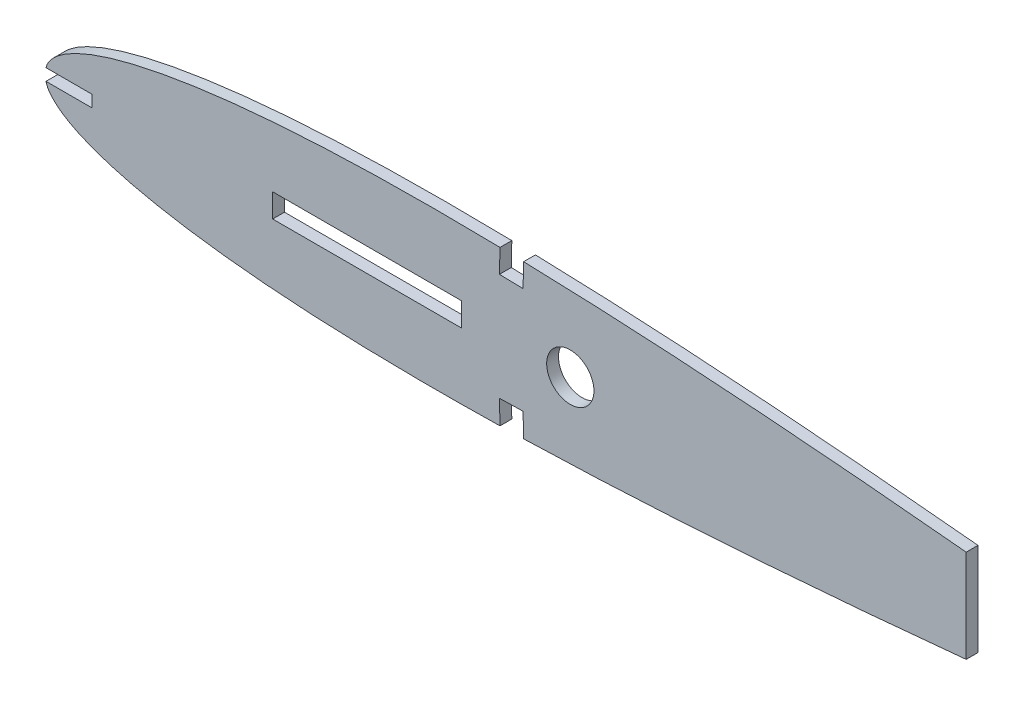
SolidWorks part; units mm, degrees
material "Plywood"
ref_plane "Front Plane" through (0, 0, 0) normal (0, 0, 1) x (1, 0, 0)
ref_plane "Top Plane" through (0, 0, 0) normal (0, 1, 0) x (1, 0, 0)
ref_plane "Right Plane" through (0, 0, 0) normal (1, 0, 0) x (0, 0, -1)
curve "Curve1"
  spline degree 3 poles (318.77, 0, 0) (318.6165, 0.178, 0) (318.1279, 0.7447, 0) (316.4159, 0.5798, 0) (314.0794, 1.1239, 0) (310.6457, 1.4976, 0) (306.3402, 2.1168, 0) (301.1057, 2.7975, 0) (295.0055, 3.5941, 0) (288.0665, 4.472, 0) (280.335, 5.4268, 0) (271.8575, 6.4421, 0) (262.6867, 7.5062, 0) (252.8789, 8.6045, 0) (242.4947, 9.7236, 0) (231.5982, 10.8496, 0) (220.2564, 11.9679, 0) (208.5394, 13.0629, 0) (196.5193, 14.1202, 0) (184.2704, 15.122, 0) (171.8679, 16.0521, 0) (159.3884, 16.8933, 0) (146.9087, 17.6278, 0) (134.5058, 18.2372, 0) (122.2562, 18.7052, 0) (110.2351, 19.0165, 0) (98.5168, 19.156, 0) (87.1732, 19.1125, 0) (76.2743, 18.8777, 0) (65.8873, 18.4456, 0) (56.076, 17.8151, 0) (46.9007, 16.9881, 0) (38.4176, 15.971, 0) (30.6784, 14.7725, 0) (23.7299, 13.4051, 0) (17.6134, 11.8842, 0) (12.3615, 10.2248, 0) (8.0073, 8.4423, 0) (4.5466, 6.5486, 0) (2.0351, 4.5401, 0) (0.333, 2.3682, 0) (0.1059, 0.7528, 0) (0, 0, 0) knots 0 0 0 0 0.002092 0.00666 0.01424 0.024785 0.038227 0.054481 0.073445 0.094999 0.119006 0.145319 0.17377 0.204184 0.236371 0.270129 0.30525 0.341517 0.378701 0.416575 0.454902 0.493447 0.531971 0.570237 0.608013 0.645066 0.681178 0.71613 0.749718 0.781748 0.812037 0.840415 0.866732 0.890849 0.912652 0.932046 0.948973 0.963413 0.975421 0.985175 0.993091 1 1 1 1
sketch "Sketch2" plane through (0, 0, 0) normal (0, 0, 1) x (1, 0, 0)
  line L4 (0, 0) -> (349.25, 0) construction
  spline S1 degree 3 poles (349.25, 0) (349.0818, 0.195) (348.5465, 0.8159) (346.6708, 0.6353) (344.1109, 1.2313) (340.3489, 1.6408) (335.6317, 2.3192) (329.8967, 3.065) (323.2132, 3.9378) (315.6107, 4.8996) (307.1399, 5.9457) (297.8518, 7.058) (287.8042, 8.224) (277.0586, 9.4273) (265.6815, 10.6534) (253.743, 11.887) (241.3168, 13.1123) (228.4795, 14.3119) (215.31, 15.4703) (201.8899, 16.5679) (188.3015, 17.587) (174.6287, 18.5086) (160.9558, 19.3133) (147.3669, 19.981) (133.9461, 20.4937) (120.7755, 20.8348) (107.9367, 20.9876) (95.5085, 20.94) (83.5675, 20.6828) (72.1873, 20.2093) (61.4378, 19.5185) (51.3852, 18.6124) (42.091, 17.4981) (33.6118, 16.185) (25.9989, 14.6868) (19.2975, 13.0206) (13.5435, 11.2025) (8.7729, 9.2495) (4.9814, 7.1748) (2.2297, 4.9742) (0.3649, 2.5947) (0.116, 0.8248) (0, 0) knots 0 0 0 0 0.002092 0.00666 0.01424 0.024785 0.038227 0.054481 0.073445 0.094999 0.119006 0.145319 0.17377 0.204184 0.236371 0.270129 0.30525 0.341517 0.378701 0.416575 0.454902 0.493447 0.531971 0.570237 0.608013 0.645066 0.681178 0.71613 0.749718 0.781748 0.812037 0.840415 0.866732 0.890849 0.912652 0.932046 0.948973 0.963413 0.975421 0.985175 0.993091 1 1 1 1
  spline S2 degree 3 poles (349.25, 0) (349.0818, -0.195) (348.5465, -0.8159) (346.6708, -0.6353) (344.1109, -1.2313) (340.3489, -1.6408) (335.6317, -2.3192) (329.8967, -3.065) (323.2132, -3.9378) (315.6107, -4.8996) (307.1399, -5.9457) (297.8518, -7.058) (287.8042, -8.224) (277.0586, -9.4273) (265.6815, -10.6534) (253.743, -11.887) (241.3168, -13.1123) (228.4795, -14.3119) (215.31, -15.4703) (201.8899, -16.5679) (188.3015, -17.587) (174.6287, -18.5086) (160.9558, -19.3133) (147.3669, -19.981) (133.9461, -20.4937) (120.7755, -20.8348) (107.9367, -20.9876) (95.5085, -20.94) (83.5675, -20.6828) (72.1873, -20.2093) (61.4378, -19.5185) (51.3852, -18.6124) (42.091, -17.4981) (33.6118, -16.185) (25.9989, -14.6868) (19.2975, -13.0206) (13.5435, -11.2025) (8.7729, -9.2495) (4.9814, -7.1748) (2.2297, -4.9742) (0.3649, -2.5947) (0.116, -0.8248) (0, 0) knots 0 0 0 0 0.002092 0.00666 0.01424 0.024785 0.038227 0.054481 0.073445 0.094999 0.119006 0.145319 0.17377 0.204184 0.236371 0.270129 0.30525 0.341517 0.378701 0.416575 0.454902 0.493447 0.531971 0.570237 0.608013 0.645066 0.681178 0.71613 0.749718 0.781748 0.812037 0.840415 0.866732 0.890849 0.912652 0.932046 0.948973 0.963413 0.975421 0.985175 0.993091 1 1 1 1
  dimension "D1" = 349.25
extrude "Boss-Extrude1" add sketch "Sketch2" along normal blind 3.175
sketch "Sketch3" plane through (0, 0, 3.175) normal (0, 0, 1) x (1, 0, 0)
  line L0 (0, 0) -> (141.224, 0) construction
  line L1 (349.25, 50.8) -> (247.65, 50.8)
  line L2 (349.25, 50.8) -> (349.25, -50.8)
  line L3 (349.25, -50.8) -> (247.65, -50.8)
  line L4 (247.65, 50.8) -> (247.65, -50.8)
  line L5 (0, 1.5875) -> (12.7, 1.5875)
  line L6 (0, 1.5875) -> (0, -1.5875)
  line L7 (0, -1.5875) -> (12.7, -1.5875)
  line L8 (12.7, 1.5875) -> (12.7, -1.5875)
  line L9 (128.6754, -20.6224) -> (128.524, -14.2742)
  line L10 (128.6754, -20.6224) -> (122.3272, -20.7738) construction
  line L11 (128.524, -14.2742) -> (122.1758, -14.4256)
  line L12 (122.3272, -20.7738) -> (122.1758, -14.4256)
  line L13 (122.3272, -20.7738) -> (128.6754, -20.6224) construction
  line L14 (122.3272, -20.7738) -> (122.6301, -33.4702)
  line L15 (128.6754, -20.6224) -> (128.9783, -33.3188)
  line L16 (122.6301, -33.4702) -> (128.9783, -33.3188)
  line L17 (128.524, 14.2742) -> (122.1758, 14.4256)
  line L18 (128.524, 14.2742) -> (128.6754, 20.6224)
  line L19 (122.1758, 14.4256) -> (122.3272, 20.7738)
  line L20 (128.6754, 20.6224) -> (122.3272, 20.7738) construction
  line L21 (122.3272, 20.7738) -> (128.6754, 20.6224) construction
  line L22 (122.3272, 20.7738) -> (122.5522, 30.2059)
  line L23 (128.6754, 20.6224) -> (128.9004, 30.0545)
  line L24 (122.5522, 30.2059) -> (128.9004, 30.0545)
  circle A0 centre (141.224, 0) radius 6.35
  spline S0 degree 3 poles (0, 0) (0.116, -0.8248) (0.3649, -2.5947) (2.2297, -4.9742) (4.9814, -7.1748) (8.7729, -9.2495) (13.5435, -11.2025) (19.2975, -13.0206) (25.9989, -14.6868) (33.6118, -16.185) (42.091, -17.4981) (51.3852, -18.6124) (61.4378, -19.5185) (72.1873, -20.2093) (83.5675, -20.6828) (95.5085, -20.94) (107.9367, -20.9876) (120.7755, -20.8348) (133.9461, -20.4937) (147.3669, -19.981) (160.9558, -19.3133) (174.6287, -18.5086) (188.3015, -17.587) (201.8899, -16.5679) (215.31, -15.4703) (228.4795, -14.3119) (241.3168, -13.1123) (253.743, -11.887) (265.6815, -10.6534) (277.0586, -9.4273) (287.8042, -8.224) (297.8518, -7.058) (307.1399, -5.9457) (315.6107, -4.8996) (323.2132, -3.9378) (329.8967, -3.065) (335.6317, -2.3192) (340.3489, -1.6408) (344.1109, -1.2313) (346.6708, -0.6353) (348.5465, -0.8159) (349.0818, -0.195) (349.25, 0) knots 0 0 0 0 0.006909 0.014825 0.024579 0.036587 0.051027 0.067954 0.087348 0.109151 0.133268 0.159585 0.187963 0.218252 0.250282 0.28387 0.318822 0.354934 0.391987 0.429763 0.468029 0.506553 0.545098 0.583425 0.621299 0.658483 0.69475 0.729871 0.763629 0.795816 0.82623 0.854681 0.880994 0.905001 0.926555 0.945519 0.961773 0.975215 0.98576 0.99334 0.997908 1 1 1 1 construction
  spline S1 degree 3 poles (349.25, 0) (349.0818, 0.195) (348.5465, 0.8159) (346.6708, 0.6353) (344.1109, 1.2313) (340.3489, 1.6408) (335.6317, 2.3192) (329.8967, 3.065) (323.2132, 3.9378) (315.6107, 4.8996) (307.1399, 5.9457) (297.8518, 7.058) (287.8042, 8.224) (277.0586, 9.4273) (265.6815, 10.6534) (253.743, 11.887) (241.3168, 13.1123) (228.4795, 14.3119) (215.31, 15.4703) (201.8899, 16.5679) (188.3015, 17.587) (174.6287, 18.5086) (160.9558, 19.3133) (147.3669, 19.981) (133.9461, 20.4937) (120.7755, 20.8348) (107.9367, 20.9876) (95.5085, 20.94) (83.5675, 20.6828) (72.1873, 20.2093) (61.4378, 19.5185) (51.3852, 18.6124) (42.091, 17.4981) (33.6118, 16.185) (25.9989, 14.6868) (19.2975, 13.0206) (13.5435, 11.2025) (8.7729, 9.2495) (4.9814, 7.1748) (2.2297, 4.9742) (0.3649, 2.5947) (0.116, 0.8248) (0, 0) knots 0 0 0 0 0.002092 0.00666 0.01424 0.024785 0.038227 0.054481 0.073445 0.094999 0.119006 0.145319 0.17377 0.204184 0.236371 0.270129 0.30525 0.341517 0.378701 0.416575 0.454902 0.493447 0.531971 0.570237 0.608013 0.645066 0.681178 0.71613 0.749718 0.781748 0.812037 0.840415 0.866732 0.890849 0.912652 0.932046 0.948973 0.963413 0.975421 0.985175 0.993091 1 1 1 1 construction
  dimension "D5" = 12.7
  dimension "D1" = 12.7
  dimension "D2" = 3.175
  dimension "D3" = 101.6
  dimension "D4" = 101.6
  dimension "D6" = 208.026
  dimension "D7" = 6.35
  dimension "D8" = 6.35
  dimension "D9" = 12.7
  dimension "D10" = 12.7
  dimension "D11" = 6.35
  dimension "D12" = 6.35
  dimension "D13" = 9.4321
extrude "Cut-Extrude1" cut sketch "Sketch3" against normal blind 5.08
sketch "Sketch4" plane through (0, 0, 3.175) normal (0, 0, 1) x (1, 0, 0)
  line L1 (61.214, 3.175) -> (112.014, 3.175)
  line L2 (61.214, 3.175) -> (61.214, -3.175)
  line L3 (61.214, -3.175) -> (112.014, -3.175)
  line L4 (112.014, 3.175) -> (112.014, -3.175)
  circle A1 centre (141.224, 0) radius 6.35 construction
  dimension "D2" = 50.8
  dimension "D4" = 29.21
  dimension "D1" = 6.35
  dimension "D3" = 3.175
extrude "Cut-Extrude2" cut sketch "Sketch4" against normal blind 5.08
